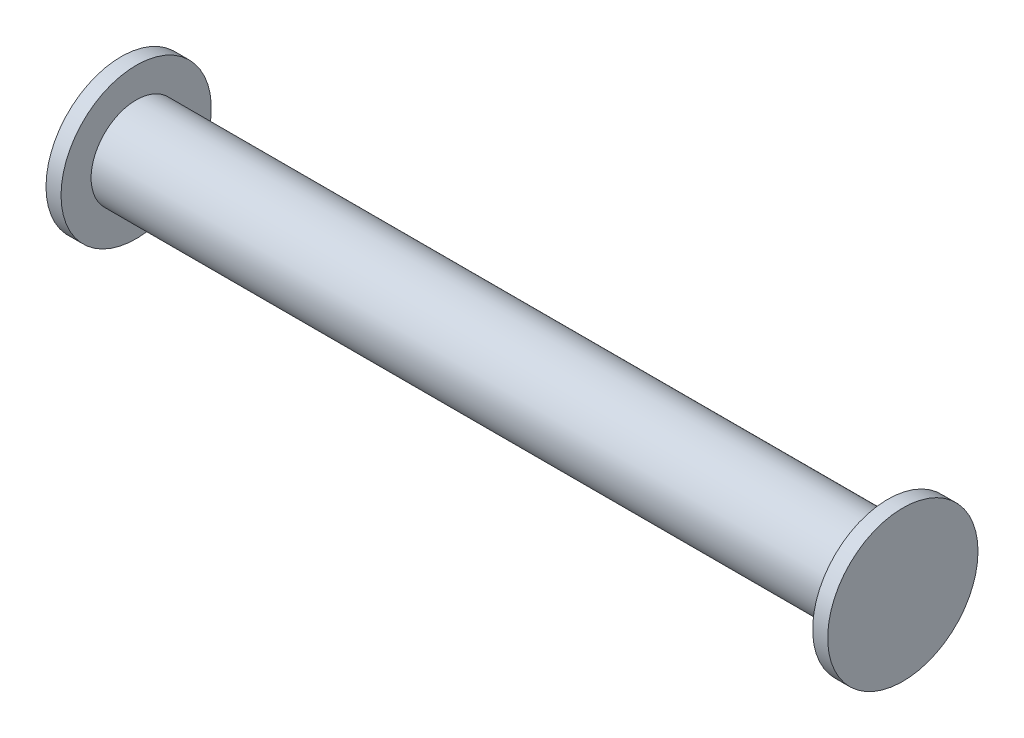
SolidWorks part; units mm, degrees
ref_plane "Front Plane"
ref_plane "Top Plane" through (0, 0, 0) normal (0, 1, 0) x (1, 0, 0)
ref_plane "Right Plane" through (0, 0, 0) normal (1, 0, 0) x (0, 0, -1)
sketch "Sketch1" plane through (0, 0, 0) normal (1, 0, 0) x (0, 0, -1)
  circle A0 centre (0, 0) radius 5
  circle A1 centre (0, 0) radius 6
  dimension "D1" = 10
  dimension "D2" = 12
extrude "Boss-Extrude1" add sketch "Sketch1" along normal mid plane 100
sketch "Sketch2" plane through (-50, 0, 0) normal (-1, 0, 0) x (0, 0, 1)
  circle A0 centre (0, 0) radius 10
  dimension "D1" = 20
extrude "Boss-Extrude4" add sketch "Sketch2" along normal blind 2 separate body
sketch "Sketch5" plane through (50, 0, 0) normal (1, 0, 0) x (0, 0, -1)
  circle A0 centre (0, 0) radius 10
extrude "Boss-Extrude5" add sketch "Sketch5" along normal blind 2 separate body
